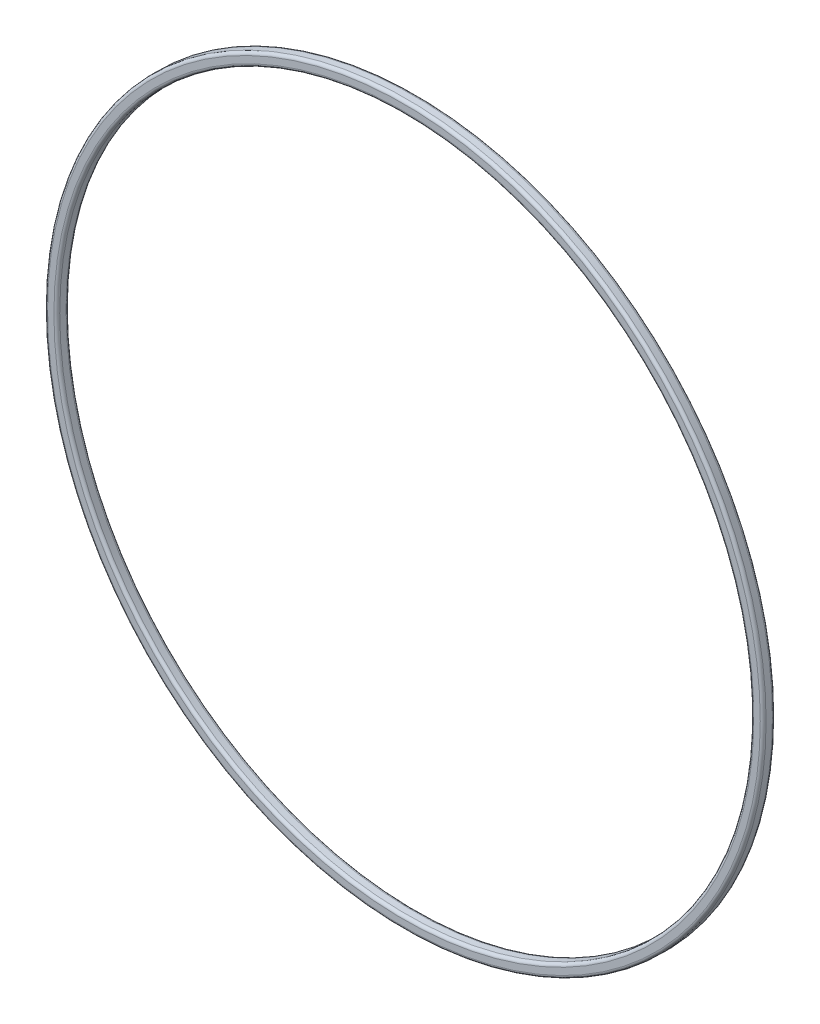
SolidWorks part; units mm, degrees
material "Rubber"
ref_plane "Front Plane" through (0, 0, 0) normal (0, 0, 1) x (1, 0, 0)
ref_plane "Top Plane" through (0, 0, 0) normal (0, 1, 0) x (1, 0, 0)
ref_plane "Right Plane" through (0, 0, 0) normal (1, 0, 0) x (0, 0, -1)
sketch "Sketch1" plane through (0, 0, 0) normal (1, 0, 0) x (0, 0, -1)
  line L0 (0, 0) -> (-35.6732, 0) construction
  line L1 (-0.8255, 93.6625) -> (0.8255, 93.6625)
  line L2 (-1.5875, 92.9005) -> (-1.5875, 91.2495)
  line L3 (-0.8255, 90.4875) -> (0.8255, 90.4875)
  line L4 (1.5875, 92.9005) -> (1.5875, 91.2495)
  line L5 (0, 93.6625) -> (0, 90.4875) construction
  arc A0 (-0.8255, 93.6625) -> (-1.5875, 92.9005) centre (-0.8255, 92.9005) ccw
  arc A1 (1.5875, 92.9005) -> (0.8255, 93.6625) centre (0.8255, 92.9005) ccw
  arc A2 (1.5875, 91.2495) -> (0.8255, 90.4875) centre (0.8255, 91.2495) cw
  arc A3 (-0.8255, 90.4875) -> (-1.5875, 91.2495) centre (-0.8255, 91.2495) cw
  point P9 (-1.5875, 93.6625)
  point P12 (1.5875, 93.6625)
  point P15 (1.5875, 90.4875)
  dimension "D3" = 0.762
  dimension "D1" = 3.175
  dimension "D2" = 3.175
  dimension "D4" = 90.4875
revolve "Revolve1" add sketch "Sketch1" angle 360 about L0
